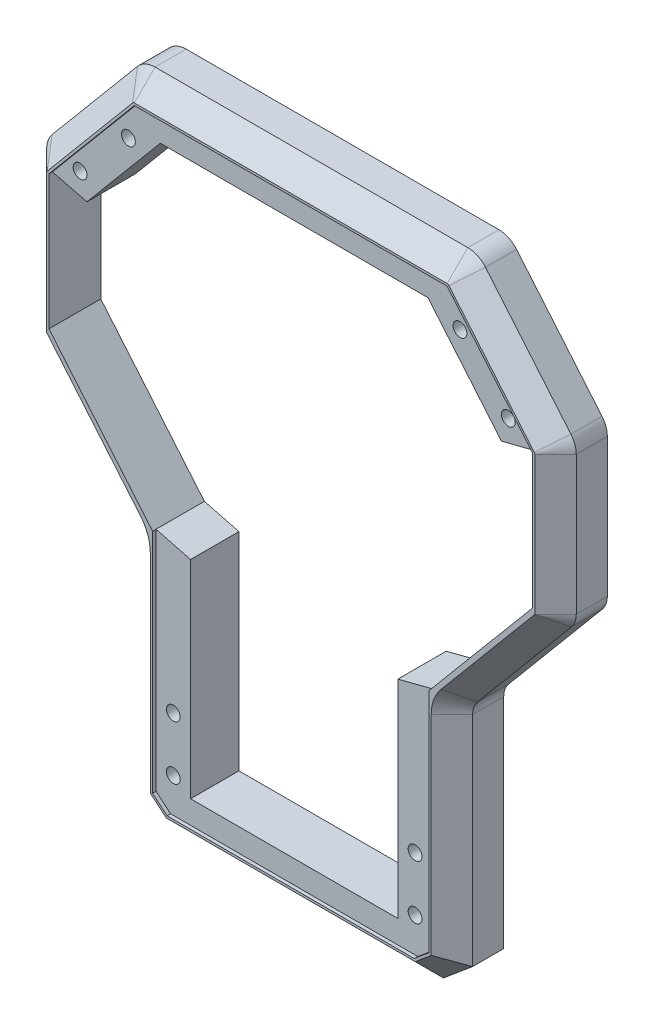
SolidWorks part; units mm, degrees
ref_plane "Plano frontal" through (0, 0, 0) normal (0, 0, 1) x (1, 0, 0)
ref_plane "Plano superior" through (0, 0, 0) normal (0, 1, 0) x (1, 0, 0)
ref_plane "Plano direito" through (0, 0, 0) normal (1, 0, 0) x (0, 0, -1)
sketch "Esboço1" plane through (0, 0, 0) normal (0, 0, 1) x (1, 0, 0)
  line L0 (-57.3196, 11.9178) -> (57.3196, 11.9178)
  line L1 (-70, 22.5579) -> (-70, 117.2967)
  line L2 (-72.1215, 123.1254) -> (-112.8785, 171.6978)
  line L3 (-115, 177.5265) -> (-115, 237.7125)
  line L4 (-67.9074, 291.9178) -> (67.9074, 291.9178)
  line L5 (0, 291.9178) -> (0, 0) construction
  line L6 (-75.5678, 288.3457) -> (-112.6604, 244.1404)
  line L7 (-90, 175.5467) -> (-90, 233.9387)
  line L8 (-90, 233.9387) -> (-58.1317, 271.9178)
  line L9 (45, 31.9178) -> (-45, 31.9178)
  line L10 (-45, 31.9178) -> (-45, 121.9178)
  line L11 (-45, 121.9178) -> (-90, 175.5467)
  line L12 (-70, 22.5579) -> (-57.3196, 11.9178)
  line L13 (70, 22.5579) -> (57.3196, 11.9178)
  line L14 (-58.1317, 271.9178) -> (58.1317, 271.9178)
  line L17 (45, 121.9178) -> (90, 175.5467)
  line L18 (45, 31.9178) -> (45, 121.9178)
  line L19 (90, 233.9387) -> (58.1317, 271.9178)
  line L20 (90, 175.5467) -> (90, 233.9387)
  line L21 (75.5678, 288.3457) -> (112.6604, 244.1404)
  line L22 (115, 177.5265) -> (115, 237.7125)
  line L23 (72.1215, 123.1254) -> (112.8785, 171.6978)
  line L24 (70, 22.5579) -> (70, 117.2967)
  arc A0 (-115, 237.7125) -> (-112.6604, 244.1404) centre (-105, 237.7125) cw
  arc A1 (-112.8785, 171.6978) -> (-115, 177.5265) centre (-105.9321, 177.5265) cw
  arc A2 (-70, 117.2967) -> (-72.1215, 123.1254) centre (-79.0679, 117.2967) ccw
  arc A3 (67.9074, 291.9178) -> (75.5678, 288.3457) centre (67.9074, 281.9178) cw
  arc A4 (-67.9074, 291.9178) -> (-75.5678, 288.3457) centre (-67.9074, 281.9178) ccw
  arc A5 (70, 117.2967) -> (72.1215, 123.1254) centre (79.0679, 117.2967) cw
  arc A6 (112.8785, 171.6978) -> (115, 177.5265) centre (105.9321, 177.5265) ccw
  arc A7 (115, 237.7125) -> (112.6604, 244.1404) centre (105, 237.7125) ccw
  point P27 (-115, 241.3522)
  point P33 (0, 31.9178)
  point P40 (0, 271.9178)
  point P46 (0, 31.9178)
  point P47 (115, 241.3522)
  point P53 (0, 280)
  dimension "D7" = 40
  dimension "D12" = 10
  dimension "D14" = 10
  dimension "D19" = 90
  dimension "D16" = 40
  dimension "D5" = 40
  dimension "D2" = 115
  dimension "D3" = 280
  dimension "D4" = 70
  dimension "D6" = 40
  dimension "D8" = 20
  dimension "D9" = 20
  dimension "D10" = 25
  dimension "D11" = 20
  dimension "D13" = 40
  dimension "D15" = 25
extrude "Ressalto-extrusão1" add sketch "Esboço1" along normal mid plane 45
chamfer "Chanfro1" distance 9 angle 45 20 edges at (0, 11.9178, 22.5) (-70, 69.9273, 22.5) (-70.5469, 120.3981, 22.5) (-92.5, 147.4116, 22.5) (0, 291.9178, 22.5) (-114.4531, 174.4251, 22.5) (-94.1141, 266.243, 22.5) (-115, 207.6195, 22.5) (70, 69.9273, 22.5) (70.5469, 120.3981, 22.5) (92.5, 147.4116, 22.5) (114.4531, 174.4251, 22.5) (115, 207.6195, 22.5) (114.3969, 241.1327, 22.5) (94.1141, 266.243, 22.5) (72.1336, 290.9809, 22.5) (-72.1336, 290.9809, 22.5) (-114.3969, 241.1327, 22.5) (-63.6598, 17.2379, 22.5) (63.6598, 17.2379, 22.5)
sketch "Esboço3" plane through (0, 0, 0) normal (0, 0, 1) x (1, 0, 0)
  line L1 (-722.7729, 507.4347) -> (416.458, 507.4347)
  line L2 (-722.7729, 507.4347) -> (-722.7729, -202.3634)
  line L3 (-722.7729, -202.3634) -> (416.458, -202.3634)
  line L4 (416.458, 507.4347) -> (416.458, -202.3634)
extrude "Corte-extrusão1" cut sketch "Esboço3" against normal up to next
sketch "Esboço4" plane through (0, 0, 22.5) normal (0, 0, 1) x (1, 0, 0)
  line L0 (-90, 175.5467) -> (-90, 233.9387)
  line L1 (-45, 121.9178) -> (-90, 175.5467)
  line L2 (-45, 121.9178) -> (-90, 175.5467) construction
  line L3 (-45, 31.9178) -> (-45, 121.9178)
  line L4 (-60, 27.221) -> (-53.6799, 21.9178)
  line L5 (0, -6.7811) -> (0, 343.2781) construction
  line L6 (-45, 31.9178) -> (45, 31.9178)
  line L7 (-61, 117.2967) -> (-61, 26.7547) construction
  line L8 (60, 27.221) -> (53.6799, 21.9178)
  line L9 (-53.6799, 21.9178) -> (53.6799, 21.9178)
  line L10 (90, 233.9387) -> (58.1317, 271.9178) construction
  line L11 (-90, 233.9387) -> (-58.1317, 271.9178)
  line L12 (-58.1317, 271.9178) -> (58.1317, 271.9178)
  line L13 (-105, 237.7125) -> (-67.9074, 281.9178)
  line L14 (-105, 237.7125) -> (-105, 179.4215)
  line L15 (-105, 179.4215) -> (-60, 125.7926)
  line L16 (-60, 125.7926) -> (-60, 27.221)
  line L17 (90, 175.5467) -> (90, 233.9387) construction
  line L18 (58.1317, 271.9178) -> (90, 233.9387)
  line L19 (-67.9074, 281.9178) -> (67.9074, 281.9178)
  line L20 (60, 125.7926) -> (60, 27.221)
  line L21 (105, 179.4215) -> (60, 125.7926)
  line L22 (105, 237.7125) -> (105, 179.4215)
  line L23 (-61, 26.7547) -> (-54.0438, 20.9178) construction
  line L24 (45, 31.9178) -> (45, 121.9178)
  line L25 (45, 121.9178) -> (90, 175.5467)
  line L26 (90, 233.9387) -> (90, 175.5467)
  line L27 (67.9074, 281.9178) -> (105, 237.7125)
  line L28 (-68.6734, 282.5606) -> (-105.766, 238.3553) construction
  line L29 (105.766, 238.3553) -> (68.6734, 282.5606) construction
  line L30 (-54.0438, 20.9178) -> (54.0438, 20.9178) construction
  line L31 (54.0438, 20.9178) -> (61, 26.7547) construction
  dimension "D1" = 15
  dimension "D2" = 10
  dimension "D3" = 9
  dimension "D4" = 15
  dimension "D5" = 1
  dimension "D6" = 10
  dimension "D7" = 1
  dimension "D8" = 1
  dimension "D9" = 1
  dimension "D10" = 15
  dimension "D11" = 1
extrude "Corte-extrusão5" cut sketch "Esboço4" against normal blind 1.5
sketch "Esboço5" plane through (0, 0, 21) normal (0, 0, 1) x (1, 0, 0)
  line L1 (-105, 237.7125) -> (-105, 179.4215) construction
  line L2 (-60, 125.7926) -> (-60, 27.221) construction
  line L3 (0, -34.4878) -> (0, 335.3959) construction
  line L4 (-53.6799, 21.9178) -> (53.6799, 21.9178) construction
  line L5 (-105, 237.7125) -> (-105, 179.4215) construction
  line L7 (67.9074, 281.9178) -> (-67.9074, 281.9178) construction
  line L8 (-60, 125.7926) -> (-60, 27.221) construction
  circle A0 centre (-93, 244) radius 3
  circle A1 centre (-52.5, 60.3962) radius 3
  circle A2 centre (-72, 266.9178) radius 3
  circle A3 centre (-52.5, 36.9178) radius 3
  circle A4 centre (52.5, 36.9178) radius 3
  circle A5 centre (72, 266.9178) radius 3
  circle A6 centre (52.5, 60.3962) radius 3
  circle A7 centre (93, 244) radius 3
  dimension "D1" = 15
  dimension "D3" = 7.5
  dimension "D4" = 7.5
  dimension "D5" = 33
  dimension "D6" = 15
  dimension "D2" = 12
extrude "Corte-extrusão6" cut sketch "Esboço5" against normal through all
sketch "Esboço7" plane through (0, 0, 0) normal (0, 0, -1) x (-1, 0, 0)
  line L1 (-73.1094, 271.4014) -> (-76.4376, 268.1988)
  line L2 (-76.4376, 268.1988) -> (-75.3282, 263.7152)
  line L3 (-75.3282, 263.7152) -> (-70.8906, 262.4342)
  line L4 (-70.8906, 262.4342) -> (-67.5624, 265.6368)
  line L5 (-67.5624, 265.6368) -> (-68.6718, 270.1203)
  line L6 (-68.6718, 270.1203) -> (-73.1094, 271.4014)
  line L7 (-92.3058, 247.9814) -> (-96.1009, 246.5919)
  line L8 (-96.1009, 246.5919) -> (-96.7951, 242.6105)
  line L9 (-96.7951, 242.6105) -> (-93.6942, 240.0186)
  line L10 (-93.6942, 240.0186) -> (-89.8991, 241.4081)
  line L11 (-89.8991, 241.4081) -> (-89.2049, 245.3895)
  line L12 (-89.2049, 245.3895) -> (-92.3058, 247.9814)
  line L13 (93, 248.0415) -> (89.5, 246.0207)
  line L14 (89.5, 246.0207) -> (89.5, 241.9793)
  line L15 (89.5, 241.9793) -> (93, 239.9585)
  line L16 (93, 239.9585) -> (96.5, 241.9793)
  line L17 (96.5, 241.9793) -> (96.5, 246.0207)
  line L18 (96.5, 246.0207) -> (93, 248.0415)
  line L19 (72.8321, 270.2805) -> (69.5038, 269.3197)
  line L20 (69.5038, 269.3197) -> (68.6718, 265.957)
  line L21 (68.6718, 265.957) -> (71.1679, 263.5551)
  line L22 (71.1679, 263.5551) -> (74.4962, 264.5159)
  line L23 (74.4962, 264.5159) -> (75.3282, 267.8786)
  line L24 (75.3282, 267.8786) -> (72.8321, 270.2805)
  line L25 (-52.5, 64.4377) -> (-56, 62.417)
  line L26 (-56, 62.417) -> (-56, 58.3755)
  line L27 (-56, 58.3755) -> (-52.5, 56.3548)
  line L28 (-52.5, 56.3548) -> (-49, 58.3755)
  line L29 (-49, 58.3755) -> (-49, 62.417)
  line L30 (-49, 62.417) -> (-52.5, 64.4377)
  line L31 (52.5, 64.4377) -> (49, 62.417)
  line L32 (49, 62.417) -> (49, 58.3755)
  line L33 (49, 58.3755) -> (52.5, 56.3548)
  line L34 (52.5, 56.3548) -> (56, 58.3755)
  line L35 (56, 58.3755) -> (56, 62.417)
  line L36 (56, 62.417) -> (52.5, 64.4377)
  line L37 (52.5, 40.9592) -> (49, 38.9385)
  line L38 (49, 38.9385) -> (49, 34.8971)
  line L39 (49, 34.8971) -> (52.5, 32.8763)
  line L40 (52.5, 32.8763) -> (56, 34.8971)
  line L41 (56, 34.8971) -> (56, 38.9385)
  line L42 (56, 38.9385) -> (52.5, 40.9592)
  line L43 (-51.546, 40.845) -> (-55.4241, 39.7076)
  line L44 (-55.4241, 39.7076) -> (-56.3781, 35.7803)
  line L45 (-56.3781, 35.7803) -> (-53.454, 32.9905)
  line L46 (-53.454, 32.9905) -> (-49.5759, 34.128)
  line L47 (-49.5759, 34.128) -> (-48.6219, 38.0553)
  line L48 (-48.6219, 38.0553) -> (-51.546, 40.845)
  circle A0 centre (-72, 266.9178) radius 4 construction
  circle A1 centre (-93, 244) radius 3.5 construction
  circle A2 centre (93, 244) radius 3.5 construction
  circle A3 centre (72, 266.9178) radius 3 construction
  circle A4 centre (-52.5, 60.3962) radius 3.5 construction
  circle A5 centre (52.5, 60.3962) radius 3.5 construction
  circle A6 centre (52.5, 36.9178) radius 3.5 construction
  circle A7 centre (-52.5, 36.9178) radius 3.5 construction
extrude "Corte-extrusão8" cut sketch "Esboço7" against normal blind 10
sketch "Esboço8" plane through (0, 0, 21) normal (0, 0, 1) x (1, 0, 0)
  line L0 (-105, 237.7125) -> (-90, 233.9387)
  line L1 (-90, 233.9387) -> (-90, 175.5467)
  line L2 (-105, 179.4215) -> (-60, 125.7926)
  line L3 (-105, 179.4215) -> (-105, 237.7125)
  line L4 (90, 233.9387) -> (105, 237.7125)
  line L5 (105, 237.7125) -> (105, 179.4215)
  line L6 (90, 175.5467) -> (45, 121.9178)
  line L7 (90, 175.5467) -> (90, 233.9387)
  line L8 (-60, 125.7926) -> (-45, 121.9178)
  line L9 (-45, 121.9178) -> (-90, 175.5467)
  line L10 (45, 121.9178) -> (60, 125.7926)
  line L11 (60, 125.7926) -> (105, 179.4215)
extrude "Corte-extrusão9" cut sketch "Esboço8" against normal through all
